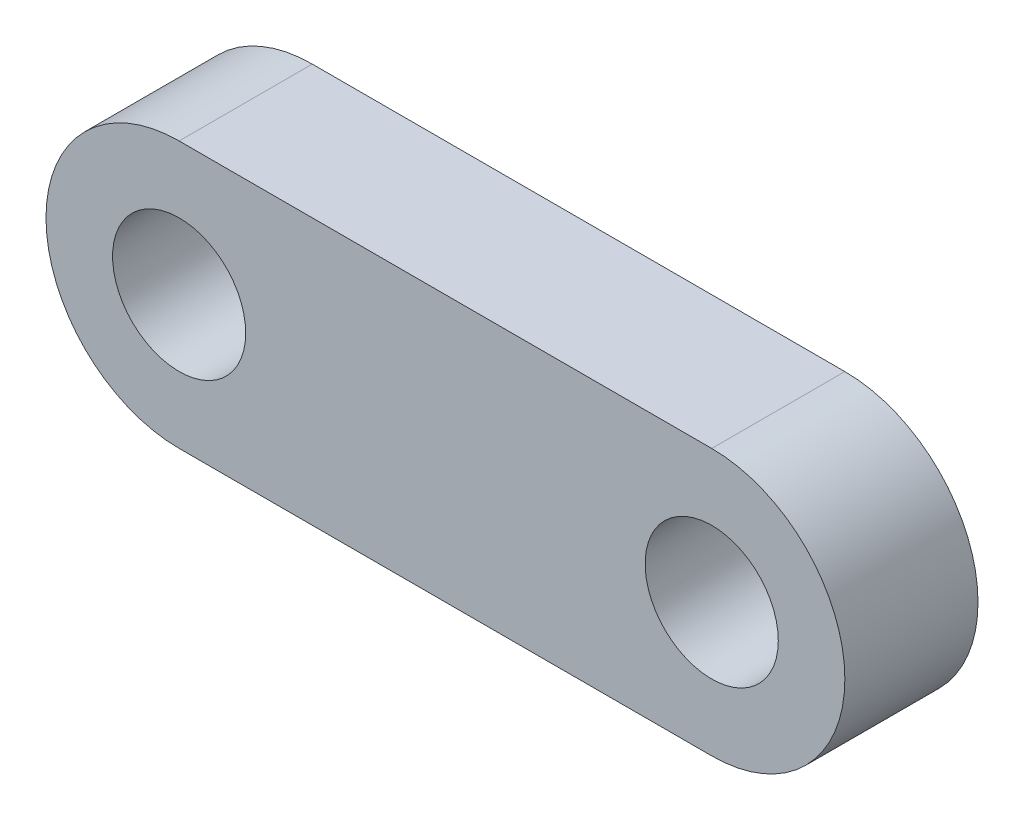
SolidWorks part; units mm, degrees
ref_plane "Front" through (0, 0, 0) normal (0, 0, 1) x (1, 0, 0)
ref_plane "Top" through (0, 0, 0) normal (0, 1, 0) x (1, 0, 0)
ref_plane "Right" through (0, 0, 0) normal (1, 0, 0) x (0, 0, -1)
sketch "profile" plane through (0, 0, 0) normal (0, 0, 1) x (1, 0, 0)
  line L0 (-112.8393, 0) -> (99.4581, 0) construction
  line L1 (-25.4, 6.35) -> (0, 6.35)
  line L2 (0, -6.35) -> (-25.4, -6.35)
  arc A0 (0, 6.35) -> (0, -6.35) centre (0, 0) cw
  arc A1 (-25.4, -6.35) -> (-25.4, 6.35) centre (-25.4, 0) cw
  dimension "D1" = 12.7
  dimension "length" = 25.4
extrude "Base-Extrude" add sketch "profile" along normal mid plane 6.35
hole_wizard "1/4 (0.250000) Diameter Hole1" positions "Sketch3" profile "Sketch2" hole size "1/4" standard "Ansi Inch" end condition through all
sketch "Sketch3" plane through (0, 0, 3.175) normal (0, 0, 1) x (1, 0, 0)
  arc A0 (-25.4, 6.35) -> (-25.4, -6.35) centre (-25.4, 0) ccw construction
  point P0 (-25.4, 0)
  point P1 (0, 0)
sketch "Sketch2" plane through (-25.4, 0, 3.175) normal (1, 0, 0) x (0, -1, 0)
  line L0 (0, 0) -> (0, 6.35)
  line L1 (0, 6.35) -> (3.175, 6.35)
  line L2 (3.175, 6.35) -> (3.175, 0)
  line L5 (3.175, 0) -> (0, 0)
  line L11 (0, -6.35) -> (0, 107.95) construction
  dimension "Thru Hole Dia." = 6.35
  dimension "Thru Hole Depth" = 6.35
